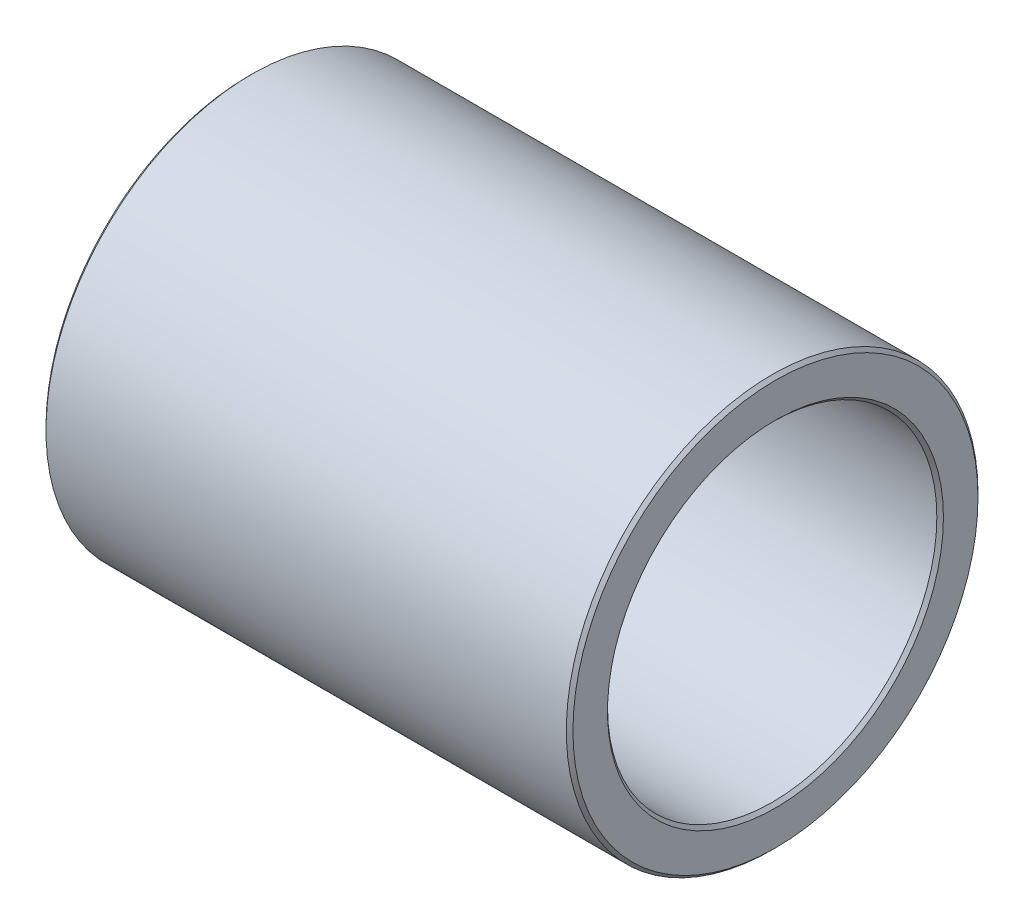
SolidWorks part; units mm, degrees
ref_plane "Front" through (0, 0, 0) normal (0, 0, 1) x (1, 0, 0)
ref_plane "Top" through (0, 0, 0) normal (0, 1, 0) x (1, 0, 0)
ref_plane "Right" through (0, 0, 0) normal (1, 0, 0) x (0, 0, -1)
sketch "Sketch1" plane through (0, 0, 0) normal (1, 0, 0) x (0, 0, -1)
  circle A0 centre (0, 0) radius 15.875
  circle A1 centre (0, 0) radius 12.7
  point P4 (3.4988, 1.9235)
  dimension "D1" = 31.75
  dimension "D2" = 25.4
extrude "Boss-Extrude1" add sketch "Sketch1" along normal blind 40.64
chamfer "Chamfer1" distance 0.254 angle 45 4 edges at (40.64, 0, -12.7) (40.64, 0, -15.875) (0, 0, -12.7) (0, 0, -15.875)
